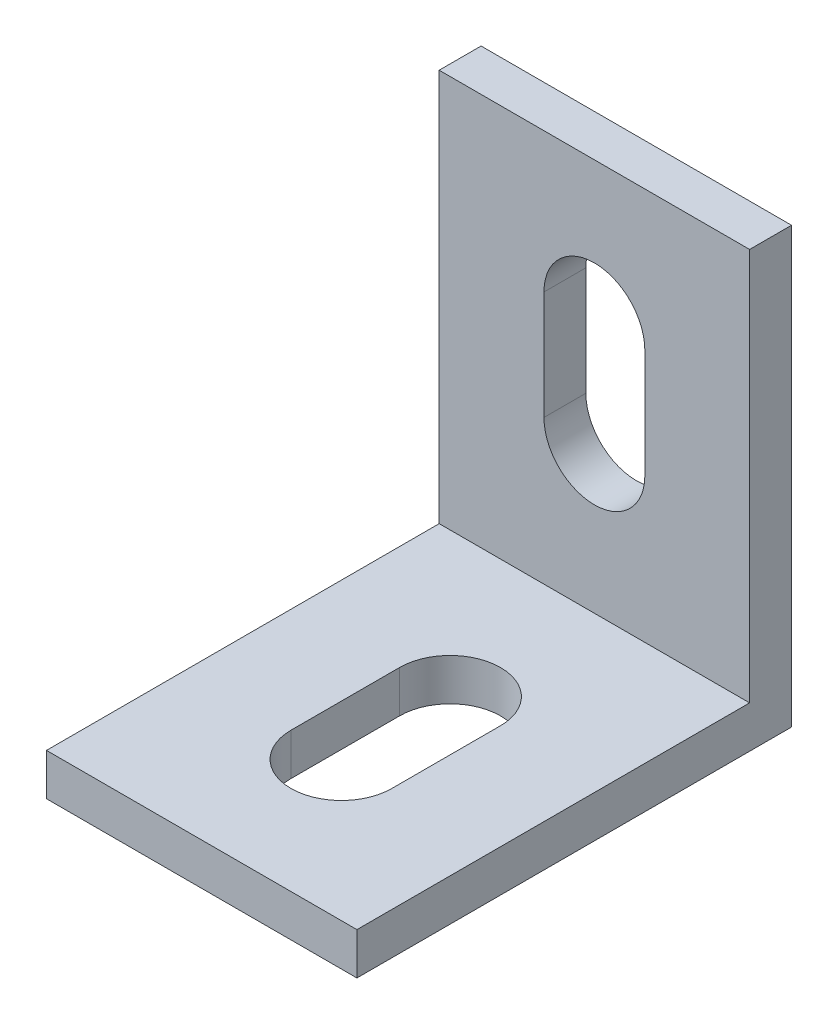
SolidWorks part; units mm, degrees
ref_plane "前视基准面" through (0, 0, 0) normal (0, 0, 1) x (1, 0, 0)
ref_plane "上视基准面" through (0, 0, 0) normal (0, 1, 0) x (1, 0, 0)
ref_plane "右视基准面" through (0, 0, 0) normal (1, 0, 0) x (0, 0, -1)
sketch "草图1" plane through (0, 0, 0) normal (0, 1, 0) x (1, 0, 0)
  line L0 (0, 14) -> (0, -1.5) construction
  line L1 (-10, 14) -> (10, 14)
  line L2 (-10, 14) -> (-10, -14)
  line L3 (-10, -14) -> (10, -14)
  line L4 (10, 14) -> (10, -14)
  line L5 (-10, 14) -> (10, -14) construction
  line L6 (-10, -14) -> (10, 14) construction
  line L7 (0, 2) -> (0, -5) construction
  line L8 (3.25, 2) -> (3.25, -5)
  line L9 (-3.25, 2) -> (-3.25, -5)
  arc A0 (3.25, 2) -> (-3.25, 2) centre (0, 2) ccw
  arc A1 (-3.25, -5) -> (3.25, -5) centre (0, -5) ccw
  point P0 (0, 0)
  point P10 (0, -1.5)
  point P15 (0, 0)
  dimension "D4" = 3.25
  dimension "D1" = 20
  dimension "D2" = 28
  dimension "D3" = 15.5
  dimension "D5" = 7
extrude "凸台-拉伸1" add sketch "草图1" along normal blind 2.7
ref_plane "基准面1" through (0, 0, -14) normal (0, 0, -1) x (-1, 0, 0)
sketch "草图2" plane through (0, 0, -14) normal (0, 0, -1) x (-1, 0, 0)
  line L0 (0, 0) -> (0, 12) construction
  line L1 (-10, 0) -> (10, 0)
  line L2 (-10, 0) -> (-10, 28)
  line L3 (-10, 28) -> (10, 28)
  line L4 (10, 0) -> (10, 28)
  line L5 (0, 12) -> (0, 19) construction
  line L6 (-3.25, 12) -> (-3.25, 19)
  line L7 (3.25, 12) -> (3.25, 19)
  arc A0 (-3.25, 12) -> (3.25, 12) centre (0, 12) ccw
  arc A1 (3.25, 19) -> (-3.25, 19) centre (0, 19) ccw
  point P8 (0, 15.5)
  dimension "D3" = 3.25
  dimension "D1" = 28
  dimension "D2" = 12
  dimension "D4" = 7
extrude "凸台-拉伸2" add sketch "草图2" against normal blind 2.7
